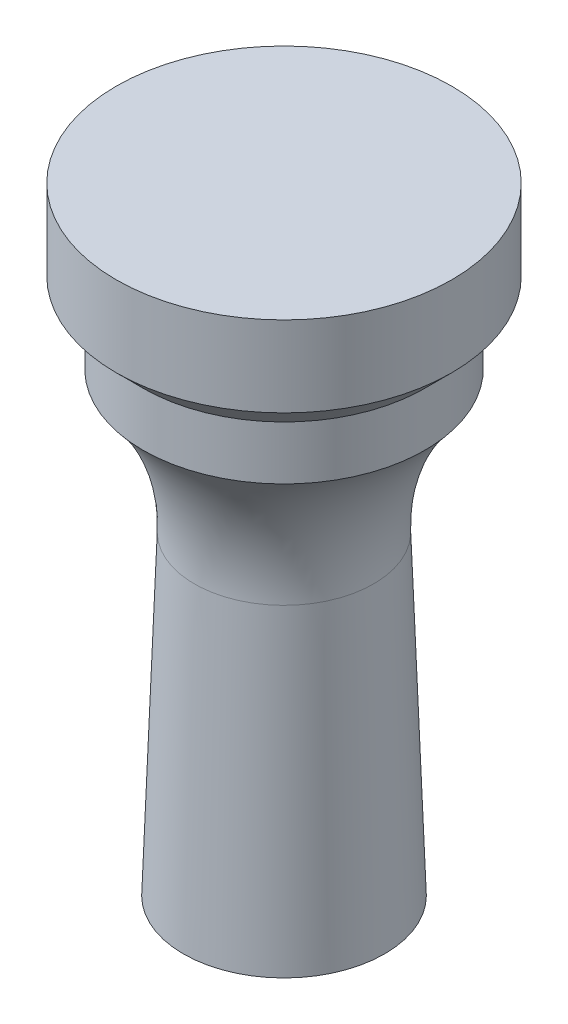
SolidWorks part; units mm, degrees
material "AISI 1045 Steel, cold drawn"
ref_plane "Plano frontal" through (0, 0, 0) normal (0, 0, 1) x (1, 0, 0)
ref_plane "Plano superior" through (0, 0, 0) normal (0, 1, 0) x (1, 0, 0)
ref_plane "Plano direito" through (0, 0, 0) normal (1, 0, 0) x (0, 0, -1)
sketch "Sketch1" plane through (0, 0, 0) normal (0, 0, 1) x (1, 0, 0)
  line L0 (0, 0) -> (0, 48) construction
  line L1 (0, 48) -> (12.5, 48)
  line L2 (12.5, 48) -> (12.5, 42)
  line L3 (12.5, 42) -> (10.5, 40)
  line L4 (10.5, 40) -> (10.5, 36)
  line L5 (0, 0) -> (2, 2)
  line L6 (2, 2) -> (7.5, 2)
  line L7 (7.5, 2) -> (6.6805, 25.4665)
  line L8 (0, 0) -> (0, 48)
  arc A0 (6.6805, 25.4665) -> (10.5, 36) centre (21.6714, 25.99) cw
  dimension "D2" = 2
  dimension "D11" = 15
  dimension "D1" = 48
  dimension "D3" = 45
  dimension "D4" = 15
  dimension "D5" = 2
  dimension "D6" = 25
  dimension "D7" = 4
  dimension "D8" = 45
  dimension "D9" = 6
  dimension "D10" = 2
revolve "Revolve1" add sketch "Sketch1" angle 360 about L0
